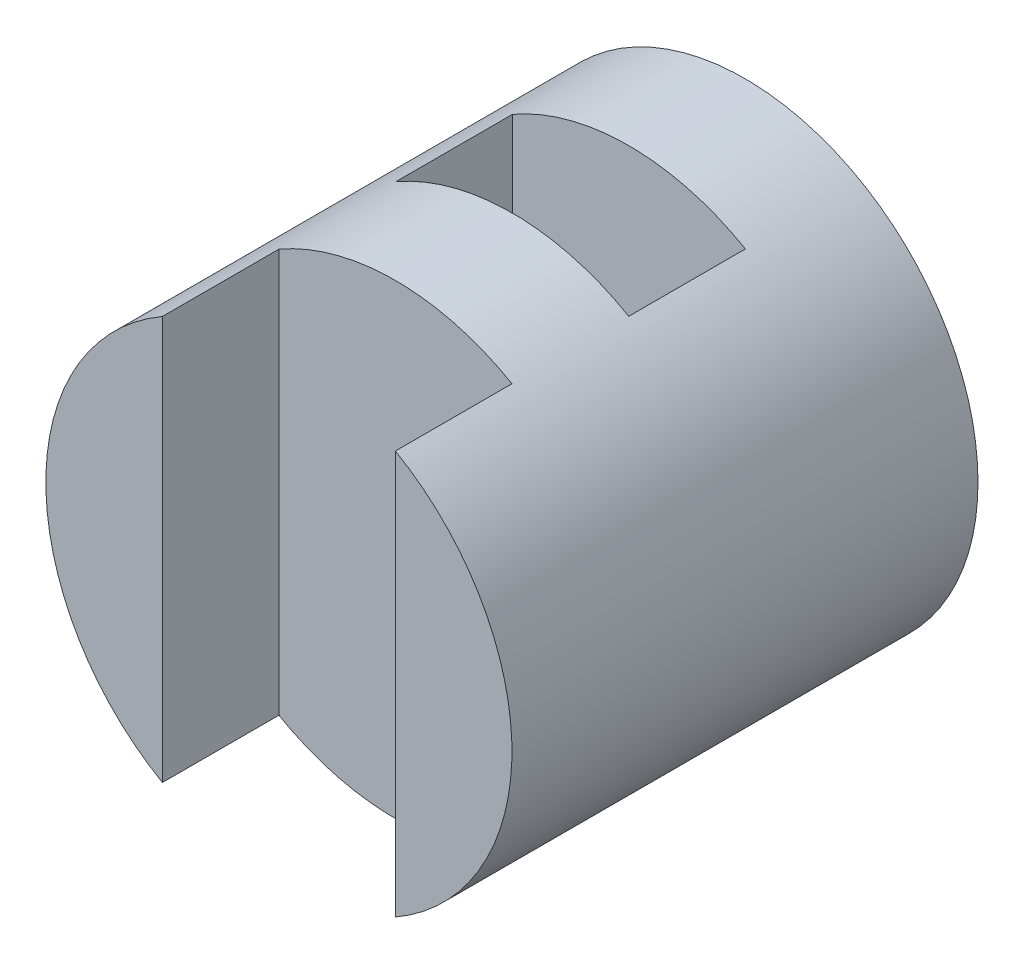
SolidWorks part; units mm, degrees
ref_plane "Front" through (0, 0, 0) normal (0, 0, 1) x (1, 0, 0)
ref_plane "Top" through (0, 0, 0) normal (0, 1, 0) x (1, 0, 0)
ref_plane "Right" through (0, 0, 0) normal (1, 0, 0) x (0, 0, -1)
sketch "Sketch1" plane through (0, 0, 0) normal (0, 0, 1) x (1, 0, 0)
  circle A0 centre (0, 0) radius 2
  dimension "D1" = 4
extrude "Boss-Extrude1" add sketch "Sketch1" along normal blind 4
sketch "Sketch2" plane through (0, 0, 0) normal (0, 1, 0) x (1, 0, 0)
  line L0 (-2, 0) -> (-2, -4) construction
  line L6 (-2, -4) -> (2, -4) construction
  line L11 (-1, -4) -> (1, -4)
  line L12 (-1, -4) -> (-1, -3)
  line L13 (-1, -3) -> (1, -3)
  line L14 (1, -4) -> (1, -3)
  line L20 (-1, -1.9973) -> (1, -1.9973)
  line L21 (-1, -1.9973) -> (-1, -0.9964)
  line L22 (-1, -0.9964) -> (1, -0.9964)
  line L23 (1, -1.9973) -> (1, -0.9964)
  dimension "D1" = 1.0009
  dimension "D2" = 2
  dimension "D7" = 2
  dimension "D8" = 1
  dimension "D9" = 1
extrude "Cut-Extrude1" cut sketch "Sketch2" against normal mid plane 10
